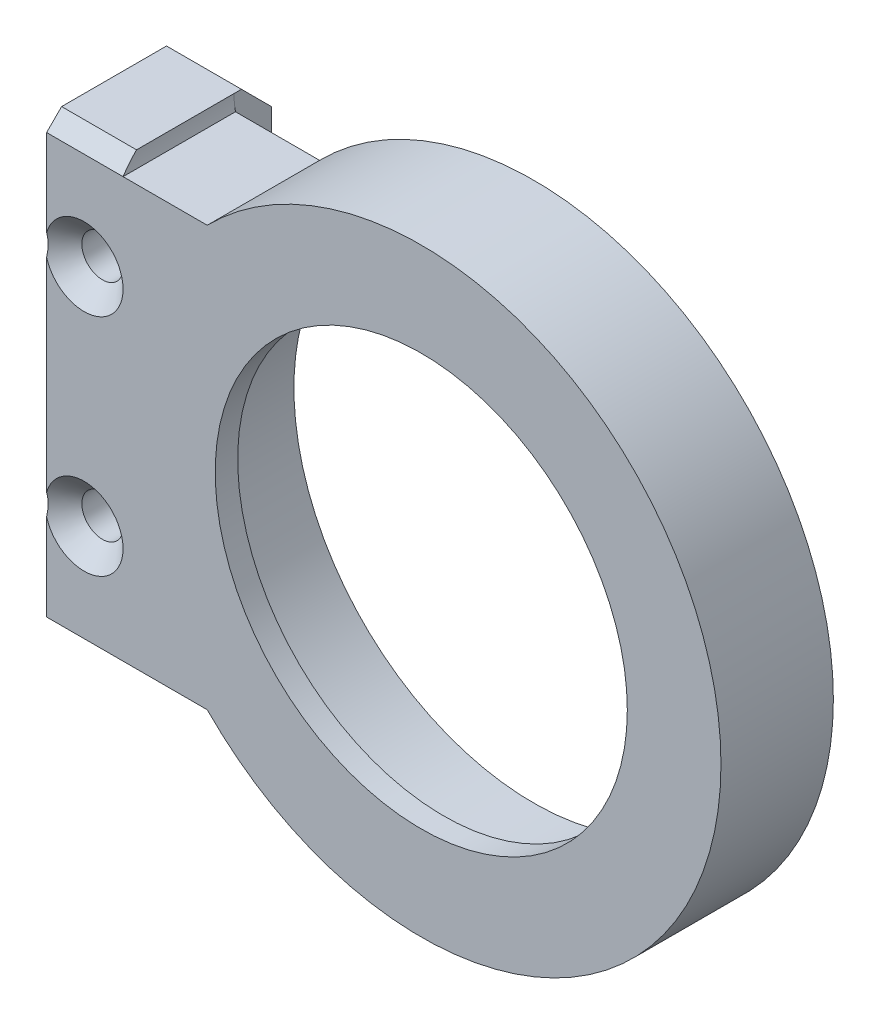
SolidWorks part; units mm, degrees
ref_plane "Front Plane" through (0, 0, 0) normal (0, 0, 1) x (1, 0, 0)
ref_plane "Top Plane" through (0, 0, 0) normal (0, 1, 0) x (1, 0, 0)
ref_plane "Right Plane" through (0, 0, 0) normal (1, 0, 0) x (0, 0, -1)
sketch "Sketch1" plane through (0, 0, 0) normal (0, 0, 1) x (1, 0, 0)
  line L1 (0, 0) -> (80, 0)
  line L2 (0, 0) -> (0, 80)
  line L3 (0, 80) -> (80, 80)
  line L4 (80, 0) -> (80, 80)
  dimension "D1" = 80
  dimension "D2" = 80
extrude "Boss-Extrude1" add sketch "Sketch1" along normal blind 15
sketch "Sketch2" plane through (0, 0, 15) normal (0, 0, 1) x (1, 0, 0)
  circle A0 centre (40, 40) radius 32
  dimension "D1" = 64
extrude "Cut-Extrude2" cut sketch "Sketch2" against normal through all
sketch "Sketch3" plane through (0, 0, 15) normal (0, 0, 1) x (1, 0, 0)
  circle A0 centre (40, 40) radius 32
  circle A1 centre (40, 40) radius 27.5
  dimension "D1" = 55
  dimension "D2" = 64
extrude "Boss-Extrude2" add sketch "Sketch3" against normal blind 3
fillet "Fillet1" radius 10 4 edges at (80, 80, 7.5) (80, 0, 7.5) (0, 0, 7.5) (0, 80, 7.5)
sketch "Sketch5" plane through (0, 0, 15) normal (0, 0, 1) x (1, 0, 0)
  line L1 (0, 70) -> (-10, 70)
  line L2 (0, 70) -> (0, 10)
  line L3 (0, 10) -> (-10, 10)
  line L4 (-10, 70) -> (-10, 10)
  dimension "D1" = 10
extrude "Boss-Extrude3" add sketch "Sketch5" against normal blind 20
sketch "Sketch6" plane through (0, 0, 15) normal (0, 0, 1) x (1, 0, 0)
  line L0 (-10, 40) -> (-5.4622, 40) construction
  line L1 (-10, 70) -> (-10, 10) construction
  line L3 (0, 70) -> (-10, 70) construction
  circle A0 centre (-5, 55) radius 2.5
  circle A2 centre (-5, 25) radius 2.5
  dimension "D2" = 15
  dimension "D4" = 5
extrude "Cut-Extrude3" cut sketch "Sketch6" against normal through all
chamfer "Chamfer1" distance 2 angle 45 2 edges at (-5, 10, 15) (-5, 70, 15)
hole_wizard "CSK for M5 Flat Head Machine Screw2" positions "Sketch9" profile "Sketch10" countersink size "M5" standard "ANSI Metric" end condition through all
sketch "Sketch9" plane through (0, 0, 15) normal (0, 0, 1) x (1, 0, 0)
  point P0 (-5, 55)
  point P3 (-5, 25)
sketch "Sketch10" plane through (-5, 55, 15) normal (1, 0, 0) x (0, -1, 0)
  line L0 (0, 0) -> (0, 20)
  line L1 (0, 20) -> (2.75, 20)
  line L2 (2.75, 20) -> (2.75, 2.45)
  line L3 (2.75, 2.45) -> (5.2, 0)
  line L5 (5.2, 0) -> (0, 0)
  line L6 (-2.75, 2.45) -> (-5.2, 0) construction
  line L11 (0, -6.35) -> (0, 107.95) construction
  dimension "Thru Hole Dia." = 5.5
  dimension "Thru Hole Depth" = 20
  dimension "Near C'Sink Dia." = 10.4
  dimension "Near C'Sink Angle" = 90
chamfer "Chamfer2" distance 4 angle 45 2 edges at (-5, 10, -5) (-5, 70, -5)
sketch "Sketch11" plane through (-10, 0, 0) normal (-1, 0, 0) x (0, 0, 1)
  line L0 (15, 40) -> (-15, 40) construction
  line L1 (15, 53.5717) -> (15, 26.4283) construction
  circle A0 centre (-15, 40) radius 15
  dimension "D2" = 30
  dimension "D1" = 30
extrude "Cut-Extrude4" cut sketch "Sketch11" against normal blind 2
sketch "Sketch12" plane through (0, 0, 15) normal (0, 0, 1) x (1, 0, 0)
  line L0 (0, 12) -> (11.4343, 12)
  line L3 (0, 68) -> (11.4343, 68)
  line L5 (0, 12) -> (0, 0)
  line L6 (0, 80) -> (80, 80)
  line L7 (0, 80) -> (0, 68)
  line L8 (0, 0) -> (80, 0)
  line L9 (80, 80) -> (80, 0)
  arc A0 (11.4343, 12) -> (11.4343, 68) centre (40, 40) ccw
  arc M8 (0.202, 12) -> (10, 0) centre (10, 10) ccw
  line M9 (10, 0) -> (70, 0)
  arc M10 (70, 0) -> (80, 10) centre (70, 10) ccw
  line M11 (80, 10) -> (80, 70)
  arc M12 (80, 70) -> (70, 80) centre (70, 70) ccw
  line M13 (70, 80) -> (10, 80)
  arc M14 (10, 80) -> (0.202, 68) centre (10, 70) ccw
  dimension "D1" = 80
extrude "Cut-Extrude7" cut sketch "Sketch12" against normal through all contours A0 L0 M8 M9 | A0 L8 M10 M11 | A0 L9 M12 M13 | A0 L6 L3 M14
